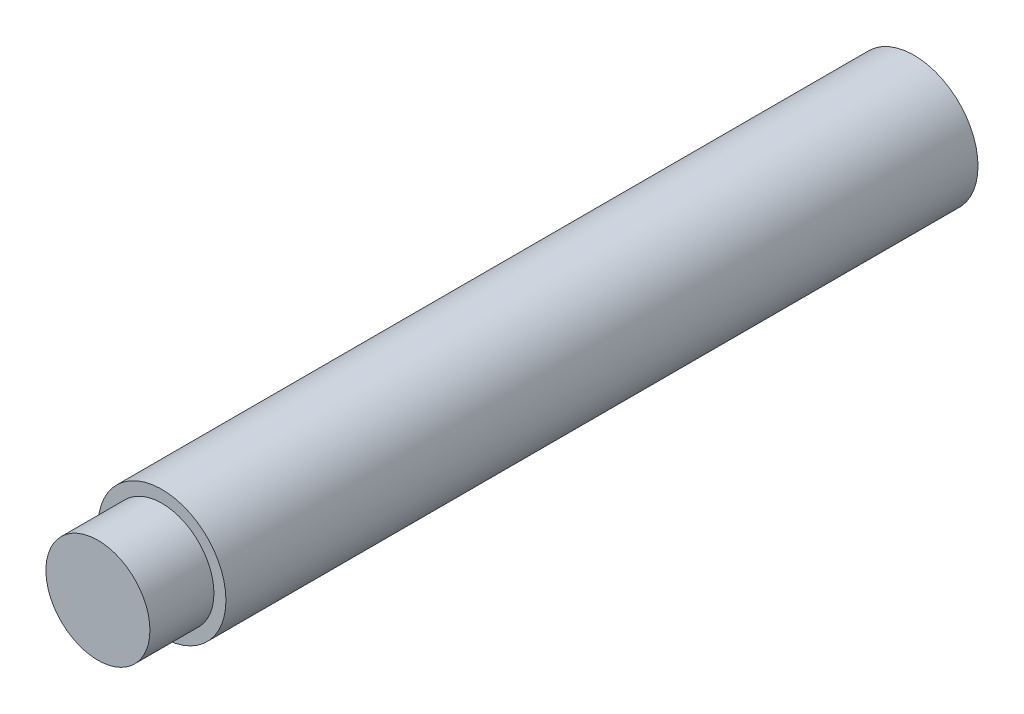
SolidWorks part; units mm, degrees
ref_plane "Front" through (0, 0, 0) normal (0, 0, 1) x (1, 0, 0)
ref_plane "Top" through (0, 0, 0) normal (0, 1, 0) x (1, 0, 0)
ref_plane "Right" through (0, 0, 0) normal (1, 0, 0) x (0, 0, -1)
other "Configuration Table"
sketch "Эскиз1" plane through (0, 0, 0) normal (0, 0, 1) x (1, 0, 0)
  circle A0 centre (0, 0) radius 4
  dimension "D1" = 8
extrude "Бобышка-Вытянуть1" add sketch "Эскиз1" along normal blind 47
sketch "Эскиз2" plane through (0, 0, 47) normal (0, 0, 1) x (1, 0, 0)
  circle A0 centre (0, 0) radius 3.25
extrude "Бобышка-Вытянуть2" add sketch "Эскиз2" along normal blind 4
